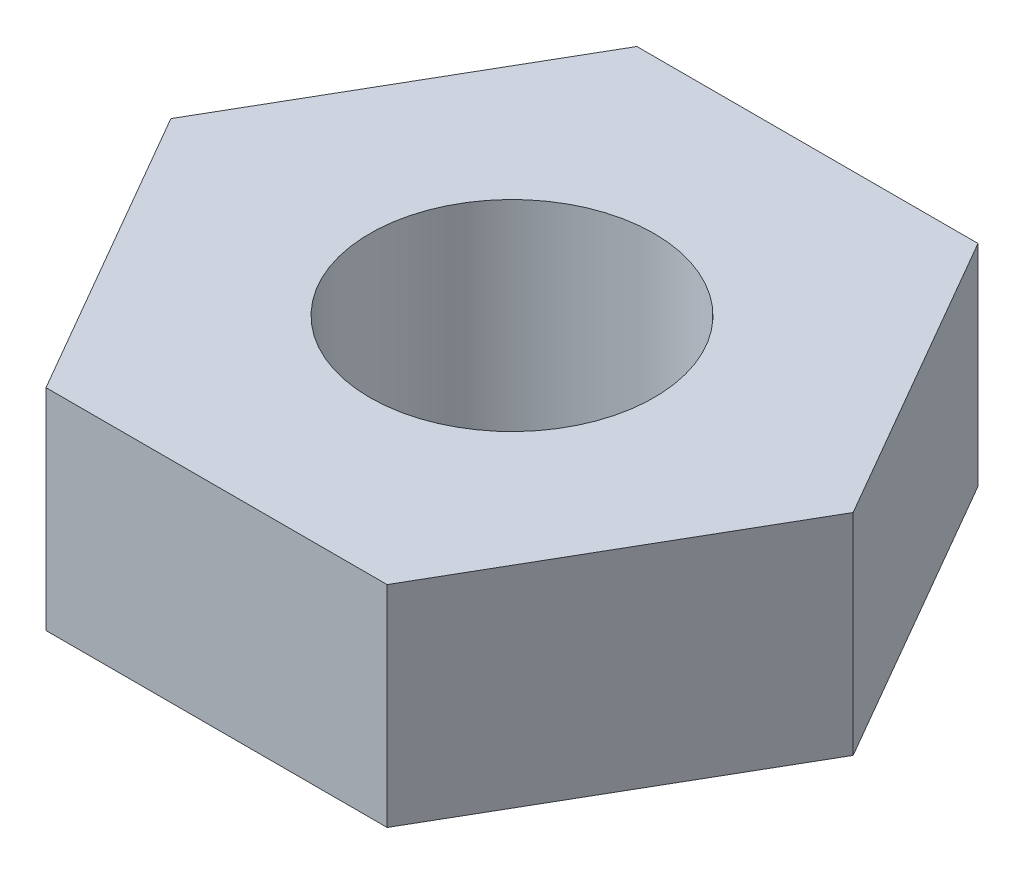
SolidWorks part; units mm, degrees
ref_plane "Front" through (0, 0, 0) normal (0, 0, 1) x (1, 0, 0)
ref_plane "Top" through (0, 0, 0) normal (0, 1, 0) x (1, 0, 0)
ref_plane "Right" through (0, 0, 0) normal (1, 0, 0) x (0, 0, -1)
sketch "Sketch1" plane through (0, 0, 0) normal (0, 1, 0) x (1, 0, 0)
  line L1 (3, 0) -> (1.5, 2.5981)
  line L2 (1.5, 2.5981) -> (-1.5, 2.5981)
  line L3 (-1.5, 2.5981) -> (-3, 0)
  line L4 (-3, 0) -> (-1.5, -2.5981)
  line L5 (-1.5, -2.5981) -> (1.5, -2.5981)
  line L6 (1.5, -2.5981) -> (3, 0)
  circle A0 centre (0, 0) radius 2.5981 construction
  dimension "D1" = 3
extrude "Boss-Extrude1" add sketch "Sketch1" along normal blind 1.85
sketch "Sketch2" plane through (0, 1.85, 0) normal (0, 1, 0) x (1, 0, 0)
  circle A0 centre (0, 0) radius 1.25
  dimension "D1" = 2.5
extrude "Cut-Extrude1" cut sketch "Sketch2" against normal blind 1.85
